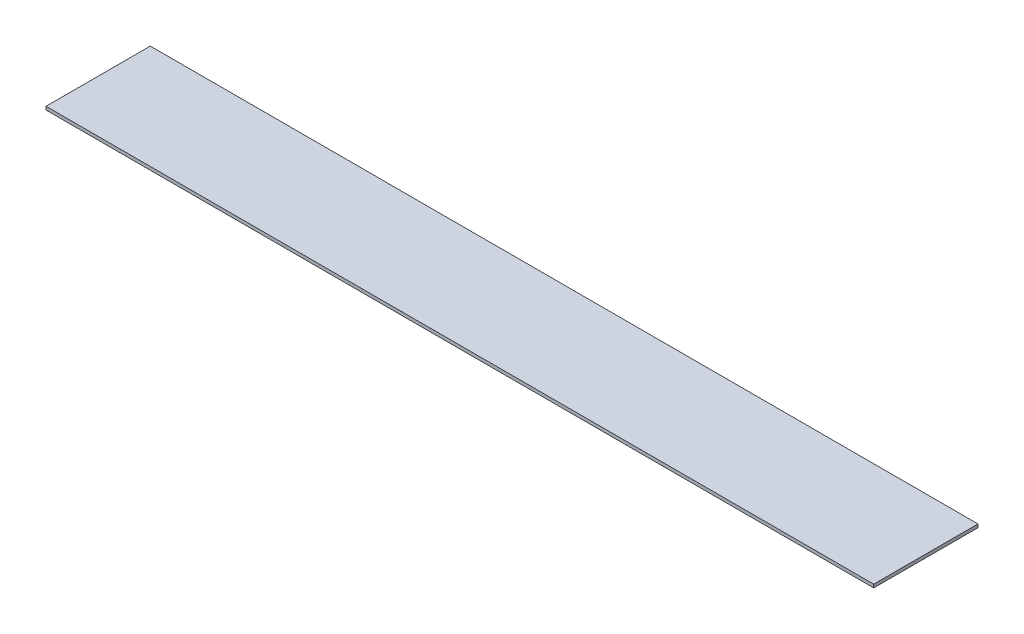
SolidWorks part; units mm, degrees
ref_plane "Front Plane" through (0, 0, 0) normal (0, 0, 1) x (1, 0, 0)
ref_plane "Top Plane" through (0, 0, 0) normal (0, 1, 0) x (1, 0, 0)
ref_plane "Right Plane" through (0, 0, 0) normal (1, 0, 0) x (0, 0, -1)
sketch "Sketch1" plane through (0, 0, 0) normal (0, 1, 0) x (1, 0, 0)
  line L1 (-63.5, -8) -> (63.5, -8)
  line L2 (-63.5, -8) -> (-63.5, 8)
  line L3 (-63.5, 8) -> (63.5, 8)
  line L4 (63.5, -8) -> (63.5, 8)
  line L5 (-63.5, -8) -> (63.5, 8) construction
  line L6 (-63.5, 8) -> (63.5, -8) construction
  point P0 (0, 0)
  dimension "D1" = 127
  dimension "D2" = 16
extrude "Boss-Extrude1" add sketch "Sketch1" along normal blind 0.5
